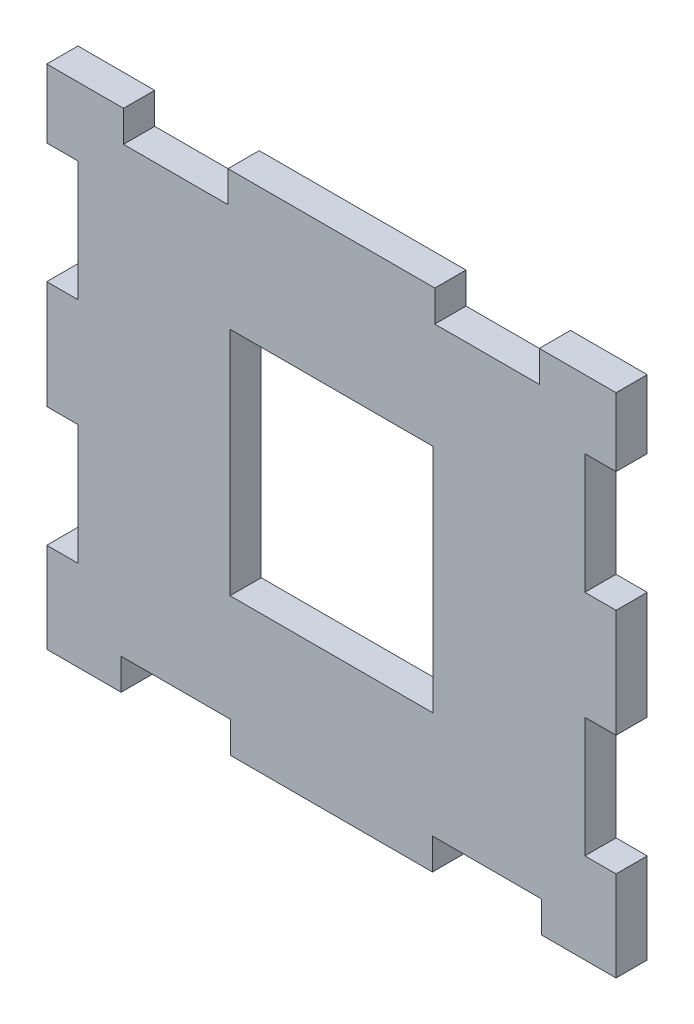
SolidWorks part; units mm, degrees
ref_plane "Plano frontal" through (0, 0, 0) normal (0, 0, 1) x (1, 0, 0)
ref_plane "Plano superior" through (0, 0, 0) normal (0, 1, 0) x (1, 0, 0)
ref_plane "Plano direito" through (0, 0, 0) normal (1, 0, 0) x (0, 0, -1)
sketch "Esboço1" plane through (0, 0, 0) normal (0, 0, 1) x (1, 0, 0)
  line L1 (-15.6644, 9.5964) -> (16.8356, 9.5964)
  line L2 (-17.6644, -0.488) -> (-17.6644, 7.212)
  line L3 (-15.6644, -18.9036) -> (16.8356, -18.9036)
  line L4 (16.8356, 9.5964) -> (16.8356, -18.9036)
  line L5 (-15.6644, 7.212) -> (-17.6644, 7.212)
  line L6 (-15.6644, -0.488) -> (-15.6644, 7.212)
  line L7 (-15.6644, -0.488) -> (-17.6644, -0.488)
  line L8 (-17.6644, -15.1242) -> (-17.6644, -7.4242)
  line L9 (-17.6644, 11.5964) -> (18.8356, 11.5964)
  line L10 (-15.6644, -7.4242) -> (-17.6644, -7.4242)
  line L11 (-17.6644, -20.9036) -> (18.8356, -20.9036)
  line L12 (18.8356, 11.5964) -> (18.8356, -20.9036)
  line L13 (-15.6644, -15.1242) -> (-15.6644, -7.4242)
  line L14 (-15.6644, -15.1242) -> (-17.6644, -15.1242)
  line L15 (-12.8944, -18.9036) -> (-12.8944, -20.9036)
  line L16 (-5.8944, -20.9036) -> (-12.8944, -20.9036)
  line L17 (7.2156, 11.5964) -> (13.9156, 11.5964)
  line L18 (7.2156, 11.5964) -> (7.2156, 9.5964)
  line L19 (7.2156, 9.5964) -> (13.9156, 9.5964)
  line L20 (13.9156, 11.5964) -> (13.9156, 9.5964)
  line L21 (-5.8944, -18.9036) -> (-5.8944, -20.9036)
  line L22 (-5.8944, -18.9036) -> (-12.8944, -18.9036)
  line L23 (-12.7444, 11.5964) -> (-12.7444, 9.5964)
  line L24 (-6.0444, 9.5964) -> (-12.7444, 9.5964)
  line L25 (-6.0444, 11.5964) -> (-6.0444, 9.5964)
  line L26 (-6.0444, 11.5964) -> (-12.7444, 11.5964)
  line L27 (-17.6644, 11.5964) -> (-17.6644, -20.9036)
  line L28 (-15.6644, 9.5964) -> (-15.6644, -18.9036)
  line L29 (7.0856, -12.0536) -> (-5.9144, -12.0536)
  line L30 (7.0856, -12.0536) -> (7.0856, 2.7464)
  line L31 (7.0856, 2.7464) -> (-5.9144, 2.7464)
  line L32 (-5.9144, -12.0536) -> (-5.9144, 2.7464)
  line L33 (7.0656, -18.9036) -> (14.0656, -18.9036)
  line L34 (7.0656, -18.9036) -> (7.0656, -20.9036)
  line L35 (7.0656, -20.9036) -> (14.0656, -20.9036)
  line L36 (14.0656, -18.9036) -> (14.0656, -20.9036)
  line L37 (16.8356, -15.1242) -> (18.8356, -15.1242)
  line L38 (16.8356, -15.1242) -> (16.8356, -7.4242)
  line L39 (16.8356, -7.4242) -> (18.8356, -7.4242)
  line L40 (18.8356, -15.1242) -> (18.8356, -7.4242)
  line L42 (16.8356, -0.488) -> (18.8356, -0.488)
  line L43 (16.8356, -0.488) -> (16.8356, 7.212)
  line L44 (16.8356, 7.212) -> (18.8356, 7.212)
  line L45 (18.8356, -0.488) -> (18.8356, 7.212)
  point P4 (0.5856, -4.6536)
  point P12 (0.5856, 9.5964)
  point P13 (0.5856, -18.9036)
  point P47 (0.5856, -4.6536)
  dimension "D2" = 28.5
  dimension "D3" = 4.92
  dimension "D4" = 2
  dimension "D5" = 14.8
  dimension "D6" = 6.7
  dimension "D7" = 13
  dimension "D8" = 2
  dimension "D14" = 7
  dimension "D15" = 4.77
  dimension "D17" = 7.7
extrude "Ressalto-extrusão1" add sketch "Esboço1" along normal blind 2 contours L1 L28 L6 L13 L3 L4 L29 L32 L31 L30 | L4 L44 L12 L9 L20 L1 | L9 L25 L1 L18 | L28 L1 L23 L9 L27 L5 | L28 L7 L27 L10 | L28 L14 L27 L11 L15 L3 | L34 L3 L21 L11 | L37 L4 L3 L36 L11 L12 | L42 L4 L39 L12
